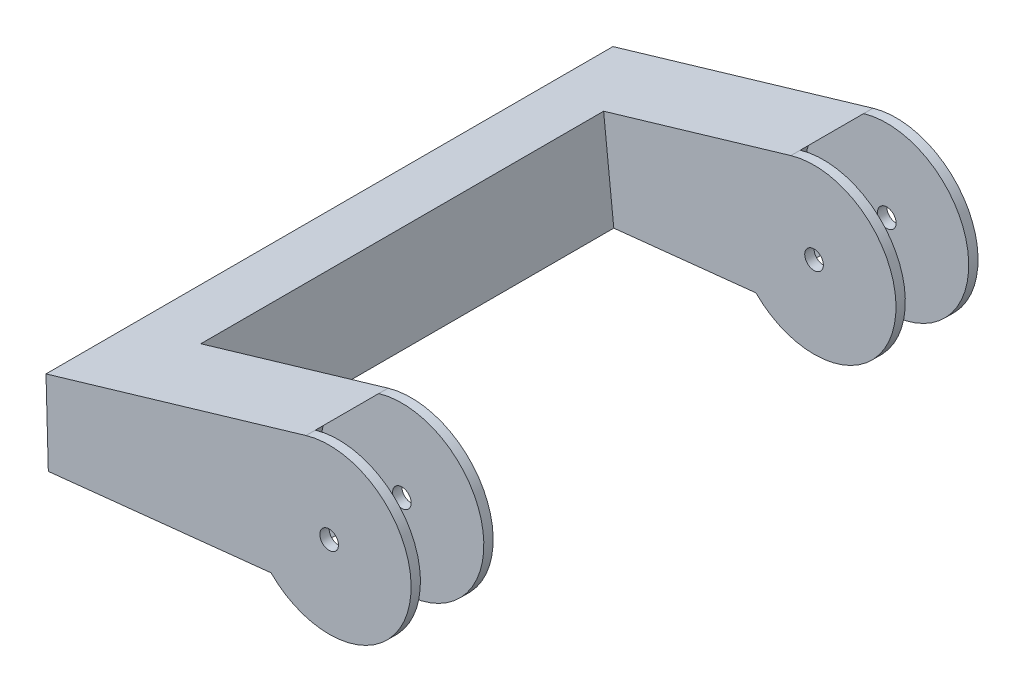
SolidWorks part; units mm, degrees
ref_plane "Front" through (0, 0, 0) normal (0, 0, 1) x (1, 0, 0)
ref_plane "Top" through (0, 0, 0) normal (0, 1, 0) x (1, 0, 0)
ref_plane "Right" through (0, 0, 0) normal (1, 0, 0) x (0, 0, -1)
sketch "Sketch1" plane through (0, 0, 0) normal (0, 0, 1) x (1, 0, 0)
  line L0 (-75.2941, -21.8019) -> (-75.9165, 0.5308)
  line L1 (-75.9165, 0.5308) -> (-6.2103, 21.0733)
  line L2 (-75.2941, -21.8019) -> (-15.5792, -15.49)
  arc A0 (-15.5792, -15.49) -> (-6.2103, 21.0733) centre (0, 0) ccw
  circle A1 centre (0, 0) radius 2.5
  circle A2 centre (0, 0) radius 2.5 construction
  dimension "D1" = 255.176
  dimension "D2" = 274.438
  dimension "D3" = 22.3414
  dimension "D4" = 72.6701
  dimension "D5" = 60.0476
extrude "Boss-Extrude1" add sketch "Sketch1" along normal mid plane 22 contours A0 L1 L0 L2
sketch "Sketch2" plane through (0, 0, 0) normal (0, 0, 1) x (1, 0, 0)
  circle A0 centre (0, 0) radius 21.9693
  arc A2 (-15.5792, -15.49) -> (-6.2103, 21.0733) centre (0, 0) ccw construction
extrude "Cut-Extrude1" cut sketch "Sketch2" against normal mid plane 17
sketch "Sketch3" plane through (0, 0, -11) normal (0, 0, -1) x (-1, 0, 0)
  line L0 (75.9165, 0.5308) -> (75.2941, -21.8019)
  line L1 (75.6053, 0.6225) -> (56.4127, 6.2786)
  line L2 (6.2103, 21.0733) -> (75.9165, 0.5308) construction
  line L3 (56.4127, 6.2786) -> (53.6859, -19.5179)
  line L4 (75.2941, -21.8019) -> (15.5792, -15.49) construction
  line L5 (53.6859, -19.5179) -> (75.2941, -21.8019)
  line L10 (15.5792, -15.49) -> (75.2941, -21.8019)
  line L11 (75.2941, -21.8019) -> (75.9165, 0.5308)
  line L12 (75.9165, 0.5308) -> (6.2103, 21.0733)
  line L13 (15.5792, -15.49) -> (75.2941, -21.8019)
  line L14 (75.2941, -21.8019) -> (75.9165, 0.5308)
  line L15 (75.6053, 0.6225) -> (6.2103, 21.0733)
  arc A1 (6.2103, 21.0733) -> (15.5792, -15.49) centre (0, 0) ccw
  arc A2 (6.2103, 21.0733) -> (15.5792, -15.49) centre (0, 0) ccw
  line M1 (15.5792, -15.49) -> (75.2941, -21.8019)
  line M2 (75.2941, -21.8019) -> (75.9165, 0.5308)
  line M3 (75.9165, 0.5308) -> (6.2103, 21.0733)
  dimension "D1" = 20
  dimension "D2" = 0
extrude "Boss-Extrude2" add sketch "Sketch3" along normal up to surface (54 mm away) contours L3 M3 M1 M2
mirror "Mirror3" about plane through (-98.1455, -3.5515, -65) normal (0, 0, 1) of "Boss-Extrude2", "Cut-Extrude1", "Boss-Extrude1"
